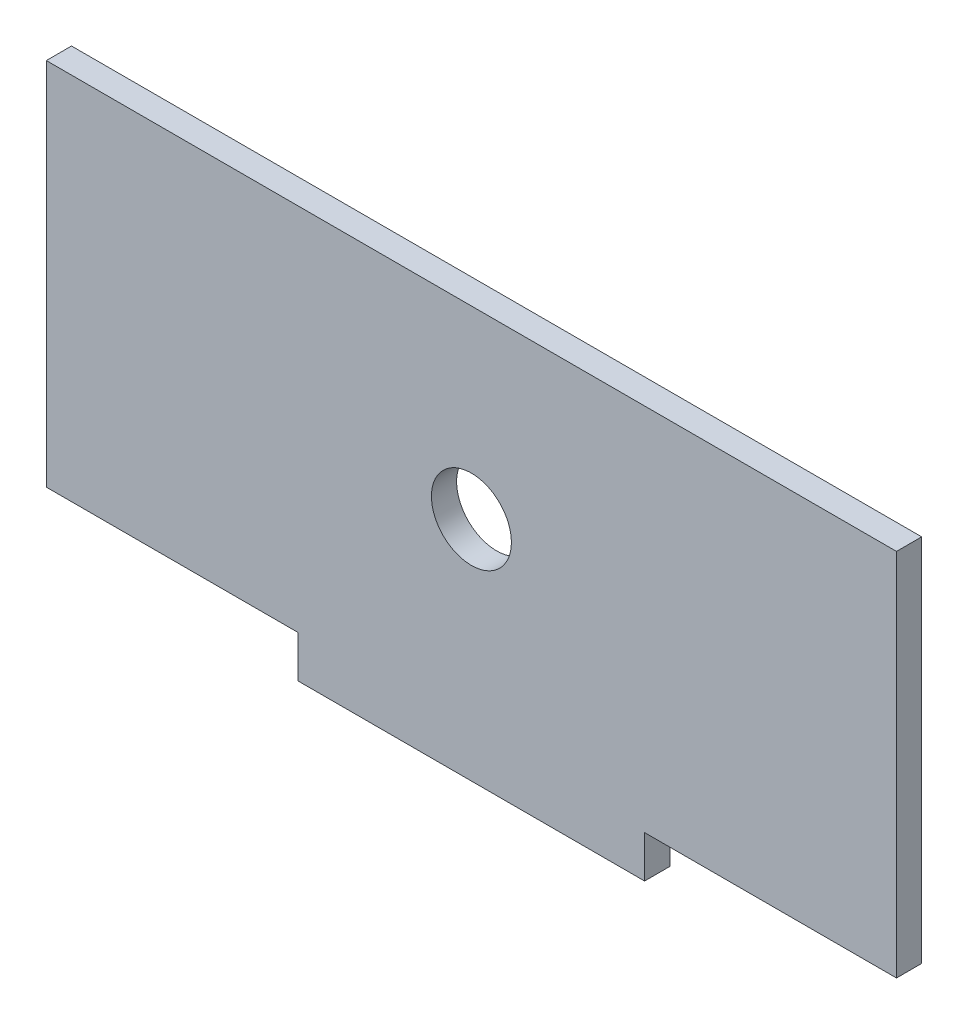
SolidWorks part; units mm, degrees
ref_plane "Front Plane" through (0, 0, 0) normal (0, 0, 1) x (1, 0, 0)
ref_plane "Top Plane" through (0, 0, 0) normal (0, 1, 0) x (1, 0, 0)
ref_plane "Right Plane" through (0, 0, 0) normal (1, 0, 0) x (0, 0, -1)
sketch "Sketch1" plane through (0, 0, 0) normal (0, 0, 1) x (1, 0, 0)
  line L0 (-50.625, 0) -> (-50.625, -44)
  line L1 (-50.625, -44) -> (-20.625, -44)
  line L2 (-20.625, -44) -> (-20.625, -49)
  line L3 (-20.625, -49) -> (20.625, -49)
  line L4 (20.625, -49) -> (20.625, -44)
  line L5 (20.625, -44) -> (50.625, -44)
  line L6 (50.625, -44) -> (50.625, 0)
  line L7 (50.625, 0) -> (-50.625, 0)
  line L8 (0, 24.4437) -> (0, -96.3194) construction
  line L9 (-50.625, -22) -> (50.625, -22) construction
  point P2 (0, 0)
  point P9 (0, -22)
  dimension "D1" = 44
  dimension "D2" = 41.25
  dimension "D3" = 5
  dimension "D4" = 30
extrude "Boss-Extrude1" add sketch "Sketch1" along normal blind 3
hole_wizard "3/8 (0.3750) Dowel Hole1" positions "Sketch2" profile "Sketch3" hole size "3/8" standard "ANSI Inch" end condition through all
sketch "Sketch2" plane through (0, 0, 3) normal (0, 0, 1) x (1, 0, 0)
  point P0 (0, -22)
sketch "Sketch3" plane through (0, -22, 3) normal (1, 0, 0) x (0, -1, 0)
  line L0 (0, 0) -> (0, 3)
  line L1 (0, 3) -> (4.7625, 3)
  line L2 (4.7625, 3) -> (4.7625, 0)
  line L5 (4.7625, 0) -> (0, 0)
  line L11 (0, -6.35) -> (0, 107.95) construction
  dimension "Thru Hole Dia." = 9.525
  dimension "Thru Hole Depth" = 3
